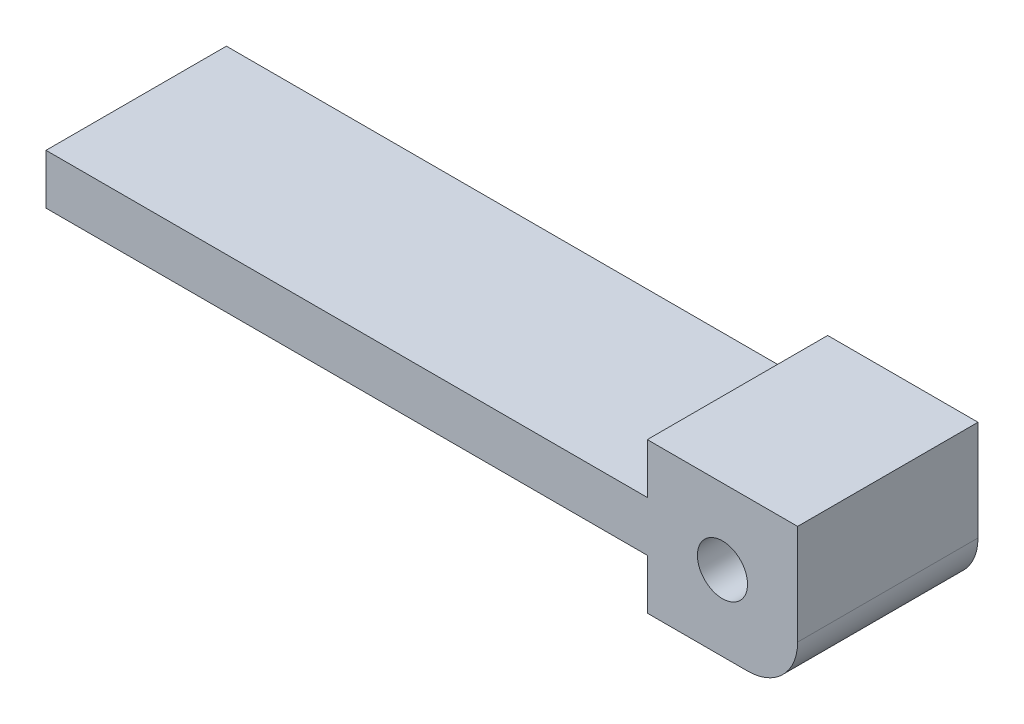
SolidWorks part; units mm, degrees
ref_plane "Ebene vorne" through (0, 0, 0) normal (0, 0, 1) x (1, 0, 0)
ref_plane "Ebene oben" through (0, 0, 0) normal (0, 1, 0) x (1, 0, 0)
ref_plane "Ebene rechts" through (0, 0, 0) normal (1, 0, 0) x (0, 0, -1)
sketch "Skizze1" plane through (0, 0, 0) normal (0, 0, 1) x (1, 0, 0)
  line L0 (0, 0) -> (-15, 0)
  line L1 (-15, 0) -> (-15, 5)
  line L2 (-15, 5) -> (-75, 5)
  line L3 (-75, 5) -> (-75, 10)
  line L4 (-75, 10) -> (-15, 10)
  line L5 (-15, 10) -> (-15, 15)
  line L6 (-15, 15) -> (0, 15)
  line L7 (0, 15) -> (0, 0)
  dimension "D1" = 15
  dimension "D2" = 5
  dimension "D3" = 60
  dimension "D4" = 5
  dimension "D5" = 5
  dimension "D6" = 15
extrude "Aufsatz-Linear austragen1" add sketch "Skizze1" along normal blind 18
sketch "Skizze2" plane through (0, 0, 18) normal (0, 0, 1) x (1, 0, 0)
  line L0 (-15, 0) -> (0, 0) construction
  line L1 (0, 0) -> (0, 15) construction
  circle A0 centre (-7.5, 7.5) radius 2.5
  point P2 (-7.5, 0)
  dimension "D1" = 5
  dimension "D2" = 7.5
  dimension "D3" = 7.5
extrude "Schnitt-Linear austragen1" cut sketch "Skizze2" against normal through all
fillet "Verrundung1" radius 5 1 edges at (0, 0, 9)
